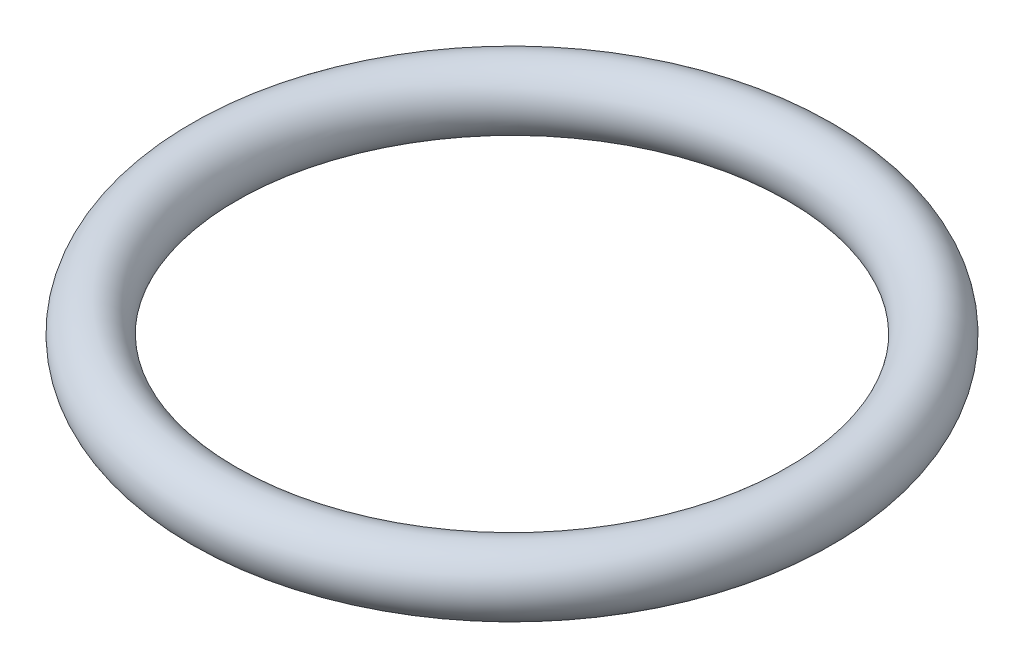
SolidWorks part; units mm, degrees
material "Резина"
ref_plane "Спереди" through (0, 0, 0) normal (0, 0, 1) x (1, 0, 0)
ref_plane "Сверху" through (0, 0, 0) normal (0, 1, 0) x (1, 0, 0)
ref_plane "Справа" through (0, 0, 0) normal (1, 0, 0) x (0, 0, -1)
ref_axis "Main" through (0, 0.825, 0) along (0, -1, 0)
sketch "Эскиз1" plane through (0, 0, 0) normal (0, 0, 1) x (1, 0, 0)
  line L0 (-5.9, 0) -> (0, 0) construction
  circle A0 centre (-6.6, 0) radius 0.7
  dimension "D1" = 1.4
  dimension "D2" = 5.9
revolve "Повернуть1" add sketch "Эскиз1" angle 360 about axis through (0, 0.825, 0) along (0, -1, 0)
